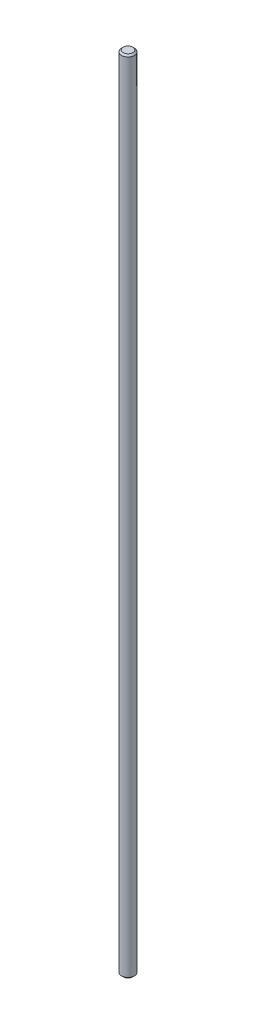
SolidWorks part; units mm, degrees
material "Plain Carbon Steel"
ref_plane "Front Plane" through (0, 0, 0) normal (0, 0, 1) x (1, 0, 0)
ref_plane "Top Plane" through (0, 0, 0) normal (0, 1, 0) x (1, 0, 0)
ref_plane "Right Plane" through (0, 0, 0) normal (1, 0, 0) x (0, 0, -1)
sketch "Sketch1" plane through (0, 0, 0) normal (0, 1, 0) x (1, 0, 0)
  circle A0 centre (0, 0) radius 4
  dimension "D1" = 8
extrude "Boss-Extrude1" add sketch "Sketch1" along normal blind 500
chamfer "Chamfer1" distance 1 angle 45 2 edges at (0, 500, 4) (0, 0, 4)
